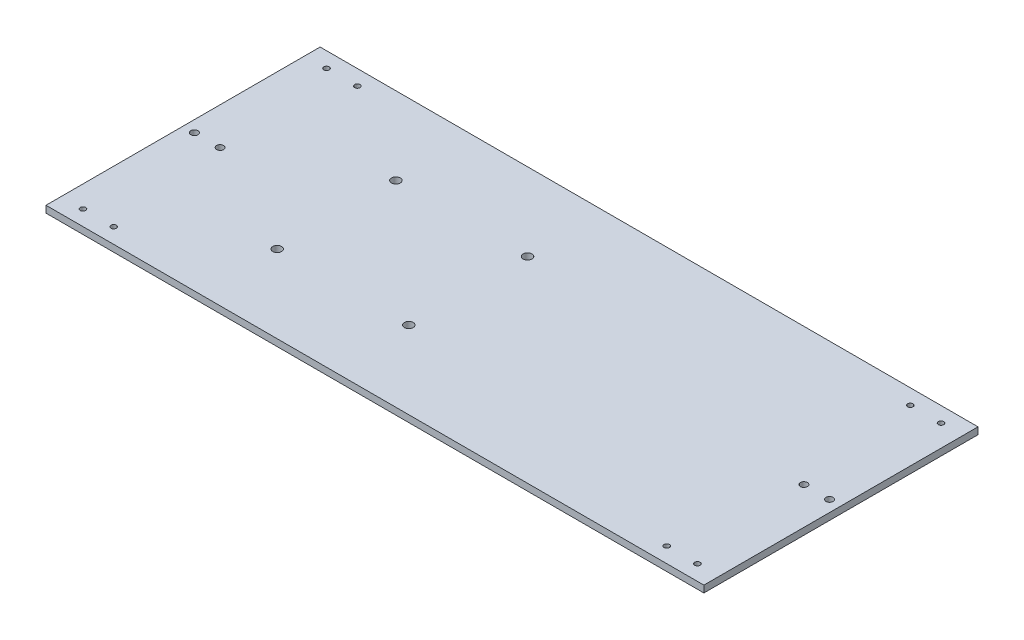
SolidWorks part; units mm, degrees
material "6061 Alloy"
ref_plane "Front Plane" through (0, 0, 0) normal (0, 0, 1) x (1, 0, 0)
ref_plane "Top Plane" through (0, 0, 0) normal (0, 1, 0) x (1, 0, 0)
ref_plane "Right Plane" through (0, 0, 0) normal (1, 0, 0) x (0, 0, -1)
sketch "Sketch1" plane through (0, 0, 0) normal (0, 1, 0) x (1, 0, 0)
  line L0 (0, 0) -> (0, 254)
  line L1 (0, 0) -> (609.6, 0)
  line L2 (0, 254) -> (609.6, 254)
  line L3 (609.6, 254) -> (609.6, 0)
  line L4 (0, 0) -> (0, 127) construction
  line L5 (0, 127) -> (50.8, 127) construction
  line L6 (50.8, 127) -> (152.4, 127) construction
  line L7 (152.4, 127) -> (254, 127) construction
  line L8 (254, 127) -> (355.6, 127) construction
  line L9 (355.6, 127) -> (457.2, 127) construction
  line L10 (457.2, 127) -> (558.8, 127) construction
  line L11 (48.6062, 14.1456) -> (20.1062, 14.1456) construction
  line L12 (34.3562, 14.1456) -> (34.3562, 239.8544) construction
  line L13 (304.8, 0) -> (304.8, 127) construction
  line L14 (575.2438, 14.1456) -> (575.2438, 127) construction
  line L15 (560.9938, 14.1456) -> (589.4938, 14.1456) construction
  line L16 (560.9938, 239.8544) -> (589.4938, 239.8544) construction
  line L17 (48.6062, 239.8544) -> (20.1062, 239.8544) construction
  line L101 (127.2, 77.5) -> (127.2, 176.5) construction
  line L102 (127.2, 176.5) -> (127.2, 182) construction
  line L103 (127.2, 77.5) -> (127.2, 72) construction
  line L104 (127.2, 72) -> (157.2, 72) construction
  line L105 (142.2, 72) -> (157.2, 72) construction
  line L106 (127.2, 182) -> (142.2, 182) construction
  line L107 (203.2, 57) -> (203.2, 197) construction
  line L108 (279.2, 182) -> (264.2, 182) construction
  line L109 (264.2, 72) -> (249.2, 72) construction
  line L110 (279.2, 72) -> (249.2, 72) construction
  line L111 (279.2, 77.5) -> (279.2, 72) construction
  line L112 (279.2, 176.5) -> (279.2, 182) construction
  line L113 (279.2, 77.5) -> (279.2, 176.5) construction
  circle A72 centre (142.2, 72) radius 4.1
  circle A73 centre (142.2, 182) radius 4.1
  circle A74 centre (264.2, 182) radius 4.1
  circle A75 centre (264.2, 72) radius 4.1
  circle A76 centre (20.1062, 14.1456) radius 2.5
  circle A77 centre (48.6062, 14.1456) radius 2.5
  circle A78 centre (560.9938, 14.1456) radius 2.5
  circle A79 centre (589.4938, 14.1456) radius 2.5
  circle A80 centre (589.4938, 239.8544) radius 2.5
  circle A81 centre (560.9938, 239.8544) radius 2.5
  circle A82 centre (48.6062, 239.8544) radius 2.5
  circle A83 centre (20.1062, 239.8544) radius 2.5
  circle A84 centre (575.2438, 127) radius 3.302
  circle A85 centre (599.0563, 127) radius 3.302
  circle A86 centre (10.5437, 127) radius 3.302
  circle A87 centre (34.3562, 127) radius 3.302
  point P35 (34.3562, 127)
extrude "Boss-Extrude1" add sketch "Sketch1" along normal blind 6.35
